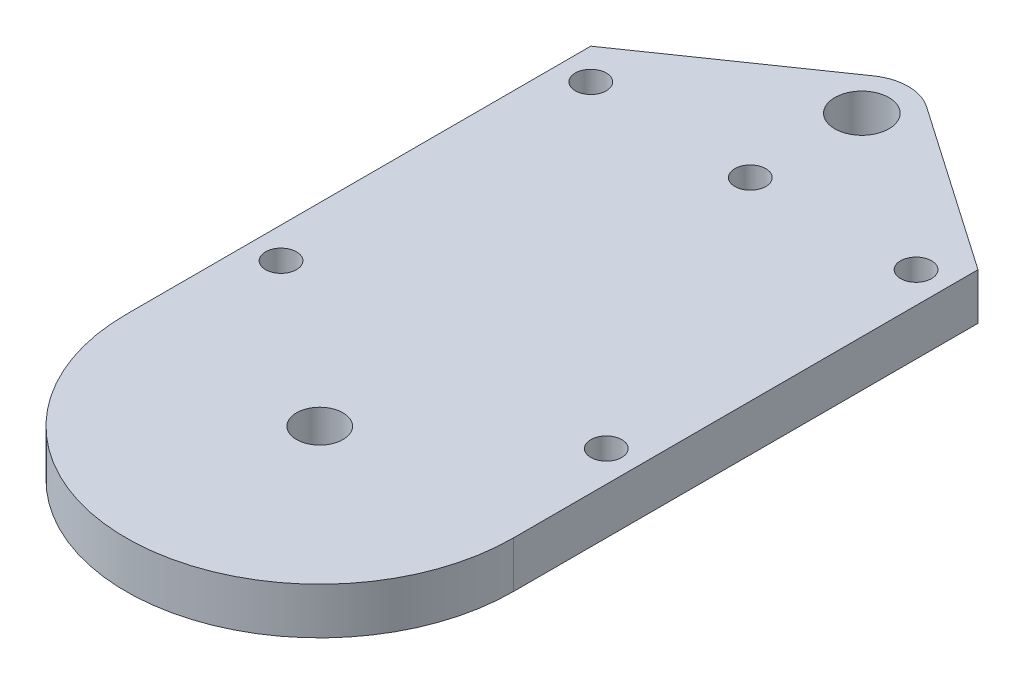
SolidWorks part; units mm, degrees
ref_plane "前视基准面" through (0, 0, 0) normal (0, 0, 1) x (1, 0, 0)
ref_plane "上视基准面" through (0, 0, 0) normal (0, 1, 0) x (1, 0, 0)
ref_plane "右视基准面" through (0, 0, 0) normal (1, 0, 0) x (0, 0, -1)
other "Configuration Table"
sketch "草图1" plane through (0, 0, 0) normal (0, 1, 0) x (1, 0, 0)
  line L0 (0, 15) -> (0, -15) construction
  line L1 (-12.5, 15) -> (12.5, 15)
  line L2 (-12.5, 15) -> (-12.5, -15)
  line L3 (-12.5, -15) -> (12.5, -15)
  line L4 (12.5, 15) -> (12.5, -15)
  line L5 (-12.5, 15) -> (12.5, -15) construction
  line L6 (-12.5, -15) -> (12.5, 15) construction
  line L7 (-12.5, 0) -> (12.5, 0) construction
  line L9 (0, 23.648) -> (-12.5, 15)
  line L10 (12.5, 15) -> (0, 23.648)
  arc A0 (-12.5, -15) -> (12.5, -15) centre (0, -15) ccw
  circle A1 centre (-10.5, 13) radius 1
  circle A2 centre (10.5, 13) radius 1
  circle A3 centre (0, -15) radius 1.5
  circle A4 centre (-10.5, -7) radius 1
  circle A5 centre (10.5, -7) radius 1
  circle A6 centre (0, 12.8) radius 1
  circle A7 centre (0, 20) radius 1.75
  point P0 (0, 0)
  point P24 (0, 0)
  dimension "D5" = 2
  dimension "D6" = 3
  dimension "D11" = 3.5
  dimension "D1" = 25
  dimension "D2" = 30
  dimension "D3" = 2
  dimension "D4" = 2
  dimension "D8" = 20
  dimension "D9" = 27.8
  dimension "D10" = 7.2
  dimension "D12" = 3
  dimension "D7" = 2
extrude "凸台-拉伸1" add sketch "草图1" along normal blind 3 contours A3 L3 L4 L1 L2 A2 A1 A4 A5 | A3 L3 A0 | L1 L10 L9 A7
fillet "圆角1" radius 3 1 edges at (0, 1.5, -23.648)
